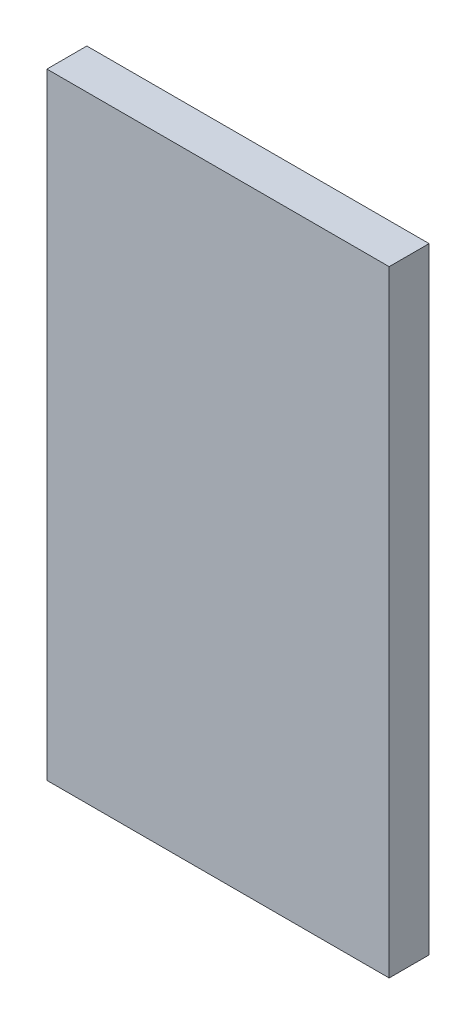
SolidWorks part; units mm, degrees
material "Custom Plastic (4)"
ref_plane "Front Plane" through (0, 0, 0) normal (0, 0, 1) x (1, 0, 0)
ref_plane "Top Plane" through (0, 0, 0) normal (0, 1, 0) x (1, 0, 0)
ref_plane "Right Plane" through (0, 0, 0) normal (1, 0, 0) x (0, 0, -1)
sketch "Radiator Cross Section" plane through (0, 0, 0) normal (0, 0, 1) x (1, 0, 0)
  line L1 (-190.5, -342.9) -> (190.5, -342.9)
  line L2 (-190.5, -342.9) -> (-190.5, 342.9)
  line L3 (-190.5, 342.9) -> (190.5, 342.9)
  line L4 (190.5, -342.9) -> (190.5, 342.9)
  line L5 (-190.5, -342.9) -> (190.5, 342.9) construction
  line L6 (-190.5, 342.9) -> (190.5, -342.9) construction
  point P0 (0, 0)
  dimension "D1" = 381
  dimension "D2" = 685.8
extrude "Radiator" add sketch "Radiator Cross Section" along normal mid plane 44.45
